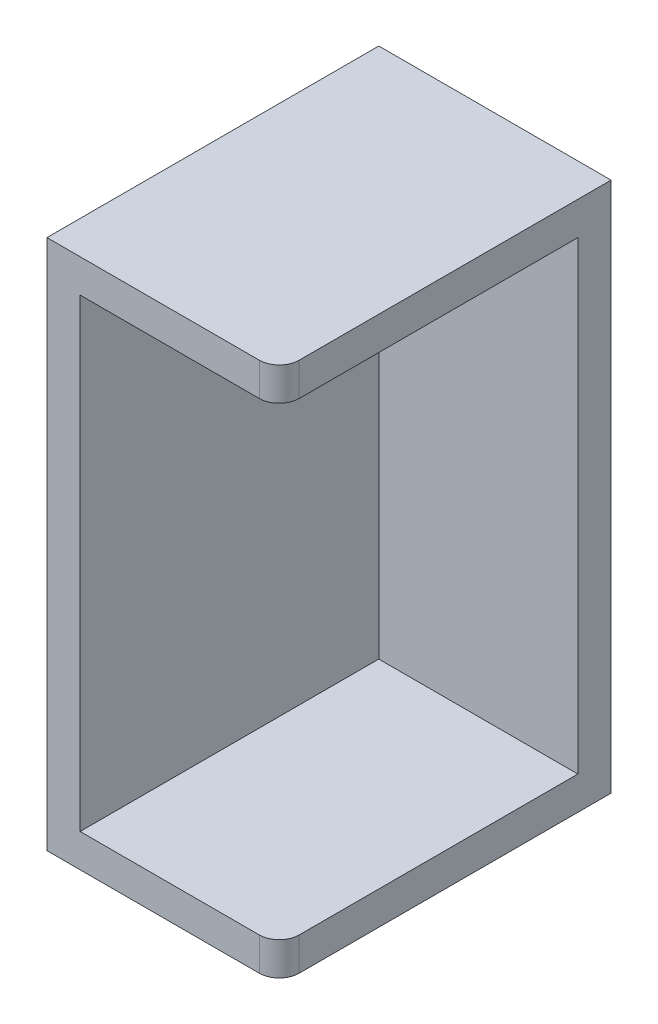
SolidWorks part; units mm, degrees
ref_plane "前基準面" through (0, 0, 0) normal (0, 0, 1) x (1, 0, 0)
ref_plane "上基準面" through (0, 0, 0) normal (0, 1, 0) x (1, 0, 0)
ref_plane "右基準面" through (0, 0, 0) normal (1, 0, 0) x (0, 0, -1)
sketch "草圖1" plane through (0, 0, 0) normal (0, 0, 1) x (1, 0, 0)
  line L1 (-35.804, 13.2919) -> (-0.804, 13.2919)
  line L2 (-35.804, 13.2919) -> (-35.804, -66.7081)
  line L3 (-35.804, -66.7081) -> (-0.804, -66.7081)
  line L4 (-0.804, 13.2919) -> (-0.804, -66.7081)
  dimension "D1" = 35
  dimension "D2" = 80
extrude "填料-伸長1" add sketch "草圖1" along normal blind 5
sketch "草圖3" plane through (0, 0, 5) normal (0, 0, 1) x (1, 0, 0)
  line L0 (-0.804, -66.7081) -> (-0.804, 13.2919) construction
  line L1 (-35.804, 13.2919) -> (-0.804, 13.2919)
  line L2 (-35.804, 13.2919) -> (-35.804, 8.2919)
  line L3 (-35.804, 8.2919) -> (-0.804, 8.2919)
  line L4 (-0.804, 13.2919) -> (-0.804, 8.2919)
  line L6 (-35.804, -66.7081) -> (-0.804, -66.7081)
  line L7 (-35.804, -66.7081) -> (-35.804, -61.7081)
  line L8 (-35.804, -61.7081) -> (-0.804, -61.7081)
  line L9 (-0.804, -66.7081) -> (-0.804, -61.7081)
  line L10 (-35.804, -66.7081) -> (-30.804, -66.7081)
  line L11 (-35.804, -66.7081) -> (-35.804, 13.2919)
  line L12 (-35.804, 13.2919) -> (-30.804, 13.2919)
  line L13 (-30.804, -66.7081) -> (-30.804, 13.2919)
  line M9 (-35.804, 13.2919) -> (-35.804, -66.7081)
  line M10 (-35.804, -66.7081) -> (-0.804, -66.7081)
  line M11 (-0.804, -66.7081) -> (-0.804, 13.2919)
  line M12 (-0.804, 13.2919) -> (-35.804, 13.2919)
  dimension "D1" = 5
  dimension "D2" = 5
  dimension "D3" = 5
extrude "填料-伸長2" add sketch "草圖3" along normal blind 45 contours L13 L3 M11 M12 | L8 L13 L3 M9 | L13 L6 L8 M11 | L13 L8 M10 M9
fillet "圓角1" radius 3 2 edges at (-0.804, 10.7919, 50) (-0.804, -64.2081, 50)
